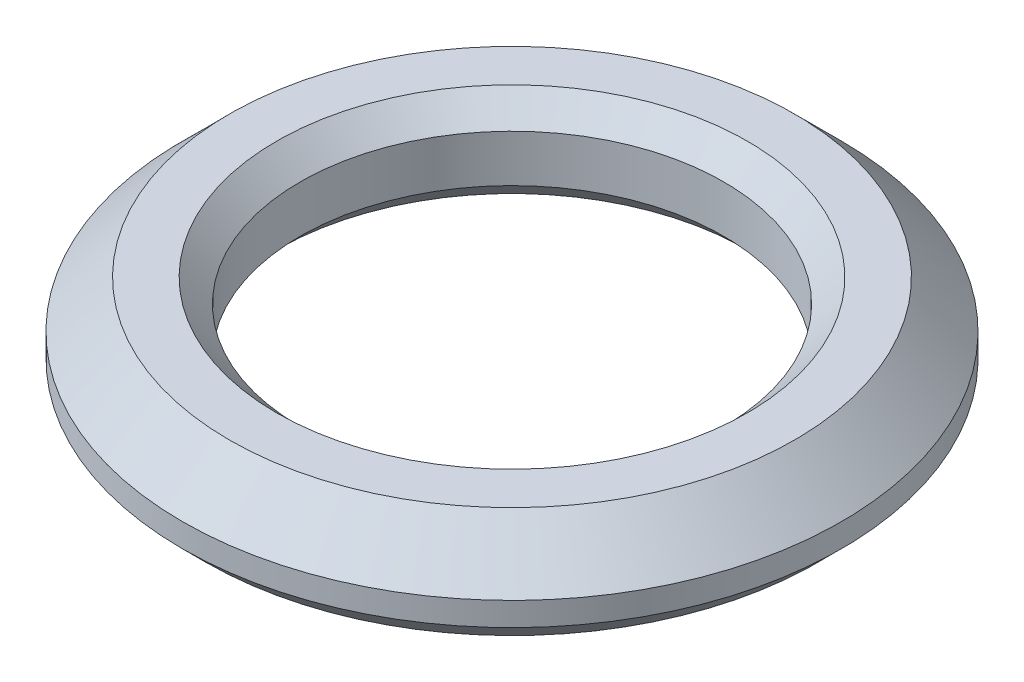
SolidWorks part; units mm, degrees
ref_plane "Front Plane" through (0, 0, 0) normal (0, 0, 1) x (1, 0, 0)
ref_plane "Top Plane" through (0, 0, 0) normal (0, 1, 0) x (1, 0, 0)
ref_plane "Right Plane" through (0, 0, 0) normal (1, 0, 0) x (0, 0, -1)
sketch "Sketch1" plane through (0, 0, 0) normal (0, 1, 0) x (1, 0, 0)
  circle A0 centre (0, 0) radius 7
  circle A1 centre (0, 0) radius 4.5
  dimension "D1" = 9
  dimension "D2" = 14
extrude "Boss-Extrude1" add sketch "Sketch1" along normal blind 2
chamfer "Chamfer1" distance 1 angle 45 1 edges at (0, 2, 7)
chamfer "Chamfer2" distance 0.5 angle 45 3 edges at (0, 2, 4.5) (0, 0, 4.5) (0, 0, 7)
